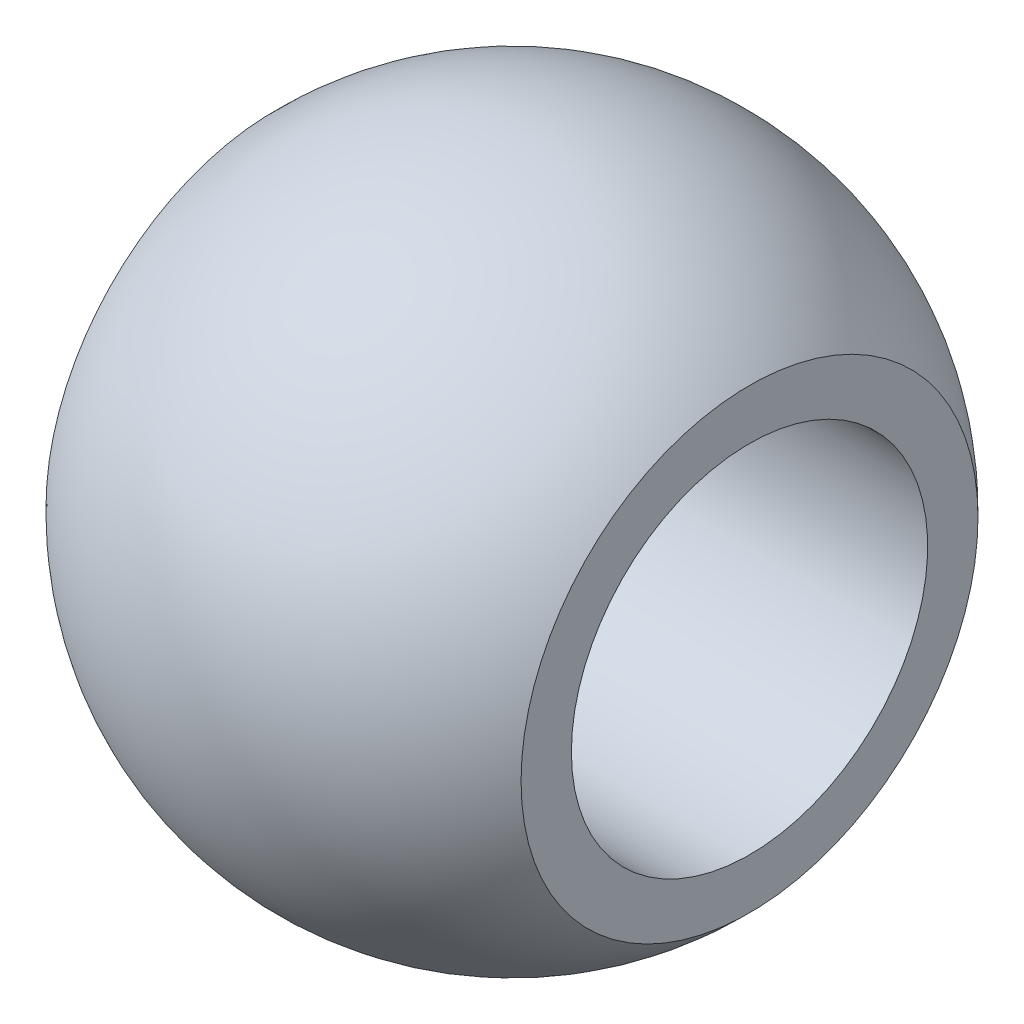
SolidWorks part; units mm, degrees
material "Plain Carbon Steel"
ref_plane "Front Plane" through (0, 0, 0) normal (0, 0, 1) x (1, 0, 0)
ref_plane "Top Plane" through (0, 0, 0) normal (0, 1, 0) x (1, 0, 0)
ref_plane "Right Plane" through (0, 0, 0) normal (1, 0, 0) x (0, 0, -1)
sketch "Sketch1" plane through (0, 0, 0) normal (0, 0, 1) x (1, 0, 0)
  line L0 (0, 0) -> (0, 38.5589) construction
  line L1 (0, 0) -> (45.1173, 0) construction
  line L2 (8, 7.6948) -> (8, 6)
  line L3 (8, 6) -> (-8, 6)
  line L4 (-8, 7.6948) -> (-8, 6)
  arc A0 (-8, 7.6948) -> (8, 7.6948) centre (0, 0) cw
  point P9 (0, 6)
  dimension "D2" = 11.1
  dimension "D1" = 12
  dimension "D3" = 16
revolve "Revolve1" add sketch "Sketch1" angle 360 about L1
